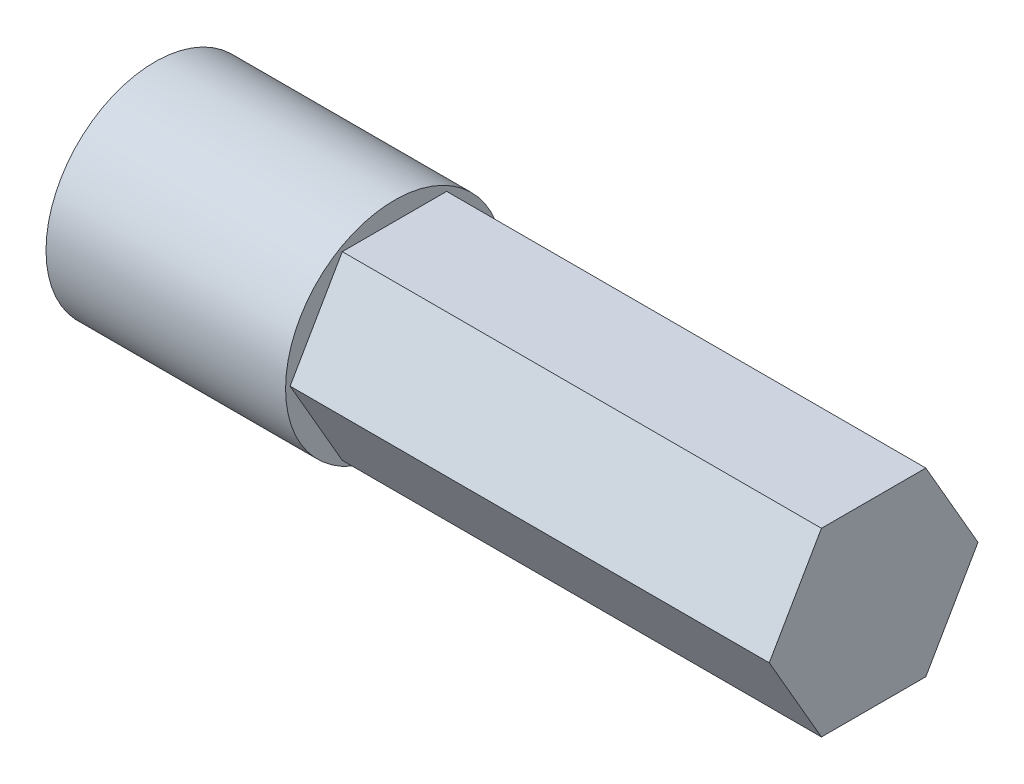
SolidWorks part; units mm, degrees
ref_plane "Front Plane" through (0, 0, 0) normal (0, 0, 1) x (1, 0, 0)
ref_plane "Top Plane" through (0, 0, 0) normal (0, 1, 0) x (1, 0, 0)
ref_plane "Right Plane" through (0, 0, 0) normal (1, 0, 0) x (0, 0, -1)
sketch "Sketch1" plane through (0, 0, 0) normal (1, 0, 0) x (0, 0, -1)
  line L1 (2.396, -4.15) -> (4.792, 0)
  line L2 (4.792, 0) -> (2.396, 4.15)
  line L3 (2.396, 4.15) -> (-2.396, 4.15)
  line L4 (-2.396, 4.15) -> (-4.792, 0)
  line L5 (-4.792, 0) -> (-2.396, -4.15)
  line L6 (-2.396, -4.15) -> (2.396, -4.15)
  circle A0 centre (0, 0) radius 4.15 construction
  dimension "D1" = 8.3
extrude "Boss-Extrude1" add sketch "Sketch1" along normal blind 22
sketch "Sketch2" plane through (0, 0, 0) normal (-1, 0, 0) x (0, 0, 1)
  circle A0 centre (0, 0) radius 5
  dimension "D1" = 10
extrude "Boss-Extrude2" add sketch "Sketch2" along normal blind 11
sketch "Sketch3" plane through (-11, 0, 0) normal (-1, 0, 0) x (0, 0, 1)
  circle A0 centre (0, 0) radius 3
  dimension "D1" = 6
extrude "Cut-Extrude1" cut sketch "Sketch3" against normal blind 11
